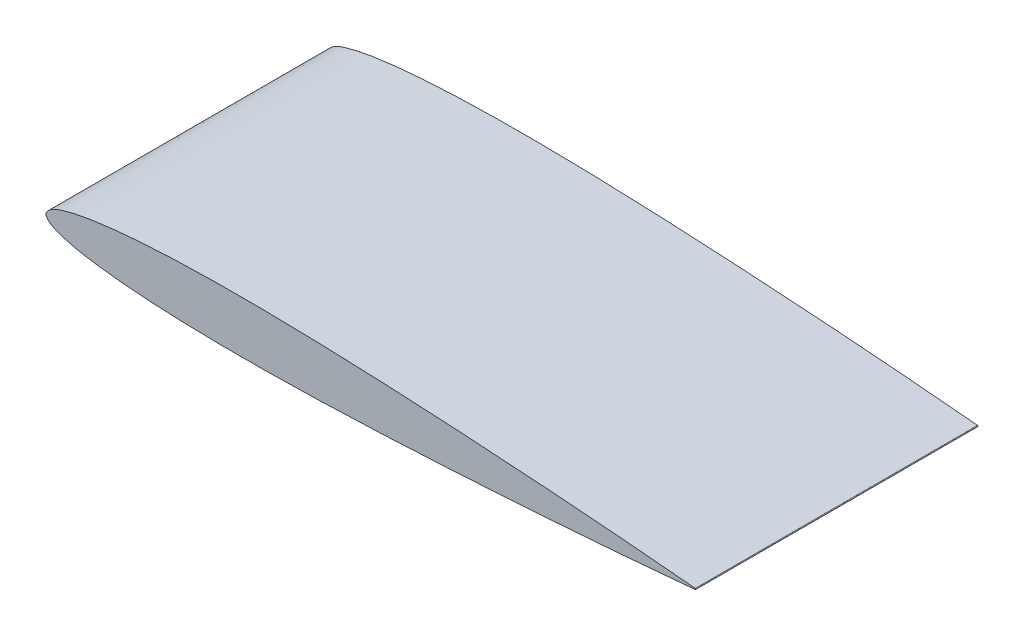
SolidWorks part; units mm, degrees
ref_plane "Front Plane" through (0, 0, 0) normal (0, 0, 1) x (1, 0, 0)
ref_plane "Top Plane" through (0, 0, 0) normal (0, 1, 0) x (1, 0, 0)
ref_plane "Right Plane" through (0, 0, 0) normal (1, 0, 0) x (0, 0, -1)
curve "Curve2"
  spline degree 3 poles (115, 0.0966, 0) (113.0835, 0.2723, 0) (109.2514, 0.6235, 0) (101.5859, 1.2775, 0) (92.0038, 2.0282, 0) (80.5034, 2.8265, 0) (69.0036, 3.521, 0) (57.5035, 4.085, 0) (46.003, 4.4884, 0) (36.417, 4.629, 0) (28.749, 4.5735, 0) (22.9974, 4.4217, 0) (17.2424, 4.1314, 0) (12.4513, 3.7233, 0) (8.6124, 3.2361, 0) (5.7426, 2.7642, 0) (3.2771, 2.1481, 0) (1.3402, 1.5191, 0) (-0.7643, 0, 0) (1.3402, -1.5191, 0) (3.2771, -2.1481, 0) (5.7426, -2.7642, 0) (8.6124, -3.2361, 0) (12.4513, -3.7233, 0) (17.2424, -4.1314, 0) (22.9974, -4.4217, 0) (28.749, -4.5735, 0) (36.417, -4.629, 0) (46.003, -4.4884, 0) (57.5035, -4.085, 0) (69.0036, -3.521, 0) (80.5034, -2.8265, 0) (92.0038, -2.0282, 0) (101.5859, -1.2775, 0) (109.2514, -0.6235, 0) (113.0835, -0.2723, 0) (115, -0.0966, 0) knots 0 0 0 0 0.024876 0.049742 0.099443 0.149112 0.198751 0.248359 0.297937 0.347491 0.372267 0.397051 0.421859 0.446731 0.45922 0.471791 0.48456 0.491195 0.5 0.508805 0.51544 0.528209 0.54078 0.553269 0.578141 0.602949 0.627733 0.652509 0.702063 0.751641 0.801249 0.850888 0.900557 0.950258 0.975124 1 1 1 1
sketch "Sketch4" plane through (0, 0, 0) normal (0, 0, 1) x (1, 0, 0)
  arc A0 (115, 0.0966) -> (115, -0.0966) centre (114.9911, 0) cw
  spline S0 degree 3 poles (681.7671, 1903.9339) (373.2712, -52.1111) (240.6786, -10.5902) (101.5859, 1.2775) (92.0038, 2.0282) (80.5034, 2.8265) (69.0036, 3.521) (57.5035, 4.085) (46.003, 4.4884) (36.417, 4.629) (28.749, 4.5735) (22.9974, 4.4217) (17.2424, 4.1314) (12.4513, 3.7233) (8.6124, 3.2361) (5.7426, 2.7642) (3.2771, 2.1481) (1.3402, 1.5191) (-0.7643, 0) (1.3402, -1.5191) (3.2771, -2.1481) (5.7426, -2.7642) (8.6124, -3.2361) (12.4513, -3.7233) (17.2424, -4.1314) (22.9974, -4.4217) (28.749, -4.5735) (36.417, -4.629) (46.003, -4.4884) (57.5035, -4.085) (69.0036, -3.521) (80.5034, -2.8265) (92.0038, -2.0282) (101.5859, -1.2775) (240.6788, 10.5902) (373.2715, 52.1112) (681.7685, -1903.9426) knots -1.704991 -1.704991 -1.704991 -1.704991 0.024876 0.049742 0.099443 0.149112 0.198751 0.248359 0.297937 0.347491 0.372267 0.397051 0.421859 0.446731 0.45922 0.471791 0.48456 0.491195 0.5 0.508805 0.51544 0.528209 0.54078 0.553269 0.578141 0.602949 0.627733 0.652509 0.702063 0.751641 0.801249 0.850888 0.900557 0.950258 0.975124 2.704993 2.704993 2.704993 2.704993 only from (115, 0.0966) to (115, -0.0966) construction
  spline S1 degree 3 poles (115, 0.0966) (113.0835, 0.2723) (109.2514, 0.6235) (101.5859, 1.2775) (92.0038, 2.0282) (80.5034, 2.8265) (69.0036, 3.521) (57.5035, 4.085) (46.003, 4.4884) (36.417, 4.629) (28.749, 4.5735) (22.9974, 4.4217) (17.2424, 4.1314) (12.4513, 3.7233) (8.6124, 3.2361) (5.7426, 2.7642) (3.2771, 2.1481) (1.3402, 1.5191) (-0.7643, 0) (1.3402, -1.5191) (3.2771, -2.1481) (5.7426, -2.7642) (8.6124, -3.2361) (12.4513, -3.7233) (17.2424, -4.1314) (22.9974, -4.4217) (28.749, -4.5735) (36.417, -4.629) (46.003, -4.4884) (57.5035, -4.085) (69.0036, -3.521) (80.5034, -2.8265) (92.0038, -2.0282) (101.5859, -1.2775) (109.2514, -0.6235) (113.0835, -0.2723) (115, -0.0966) knots 0 0 0 0 0.024876 0.049742 0.099443 0.149112 0.198751 0.248359 0.297937 0.347491 0.372267 0.397051 0.421859 0.446731 0.45922 0.471791 0.48456 0.491195 0.5 0.508805 0.51544 0.528209 0.54078 0.553269 0.578141 0.602949 0.627733 0.652509 0.702063 0.751641 0.801249 0.850888 0.900557 0.950258 0.975124 1 1 1 1
extrude "Boss-Extrude1" add sketch "Sketch4" along normal blind 50
